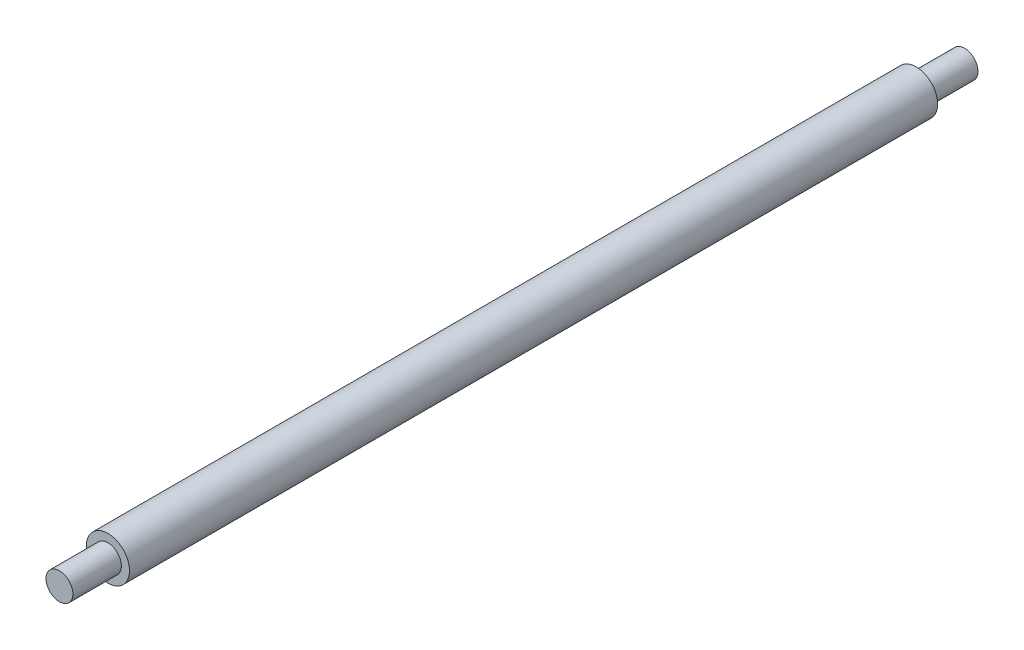
SolidWorks part; units mm, degrees
ref_plane "Front Plane" through (0, 0, 0) normal (0, 0, 1) x (1, 0, 0)
ref_plane "Top Plane" through (0, 0, 0) normal (0, 1, 0) x (1, 0, 0)
ref_plane "Right Plane" through (0, 0, 0) normal (1, 0, 0) x (0, 0, -1)
sketch "Sketch1" plane through (0, 0, 0) normal (0, 0, 1) x (1, 0, 0)
  circle A0 centre (0, 0) radius 20
extrude "Boss-Extrude1" add sketch "Sketch1" along normal blind 750
sketch "Sketch2" plane through (0, 0, 750) normal (0, 0, 1) x (1, 0, 0)
  circle A0 centre (0, 0) radius 12.5
extrude "Boss-Extrude2" add sketch "Sketch2" along normal blind 45
sketch "Sketch3" plane through (0, 0, 0) normal (0, 0, -1) x (-1, 0, 0)
  circle A0 centre (0, 0) radius 12.5
extrude "Boss-Extrude3" add sketch "Sketch3" along normal blind 45
